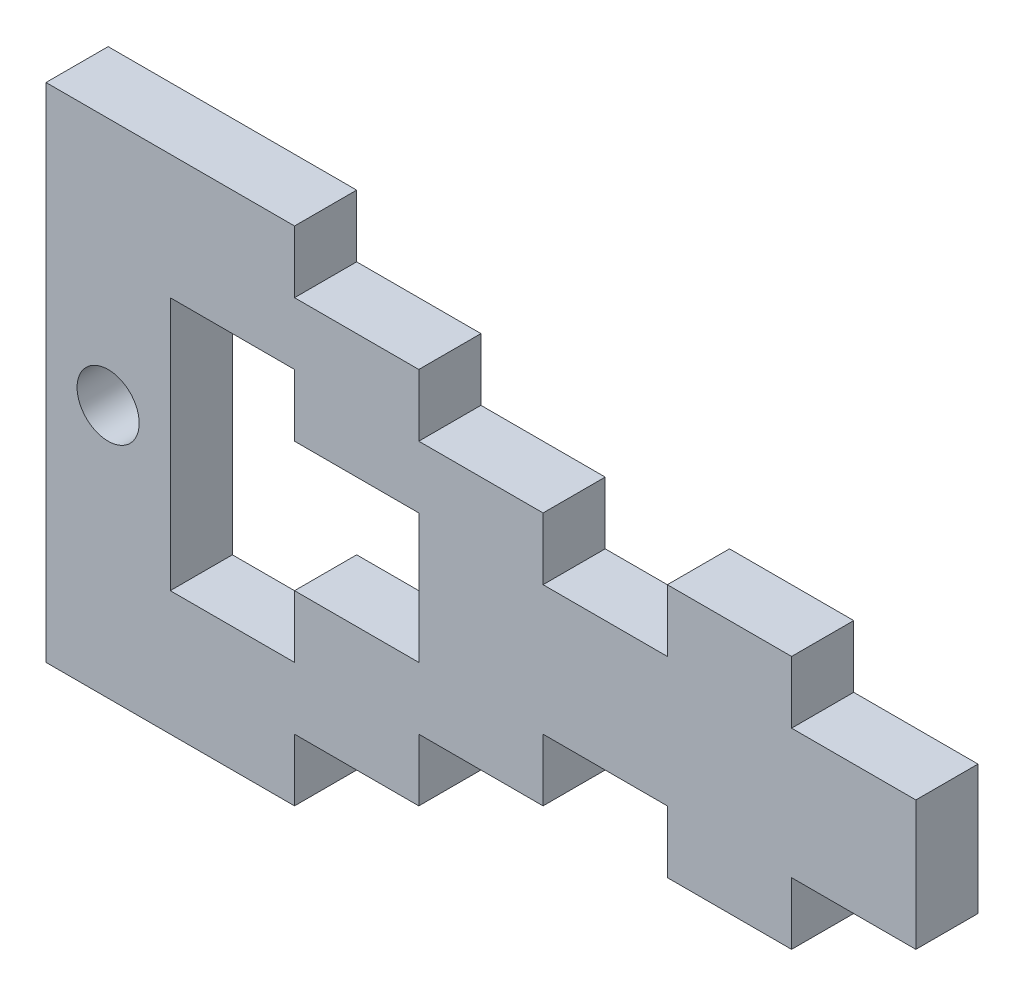
SolidWorks part; units mm, degrees
ref_plane "Front Plane" through (0, 0, 0) normal (0, 0, 1) x (1, 0, 0)
ref_plane "Top Plane" through (0, 0, 0) normal (0, 1, 0) x (1, 0, 0)
ref_plane "Right Plane" through (0, 0, 0) normal (1, 0, 0) x (0, 0, -1)
sketch "Model" plane through (0, 0, 0) normal (0, 0, 1) x (1, 0, 0)
  line L0 (3258.1067, 1248.3884) -> (3264.1067, 1248.3884)
  line L1 (3264.1067, 1242.1384) -> (3258.1067, 1242.1384)
  line L2 (3258.1067, 1248.3884) -> (3258.1067, 1251.3884)
  line L3 (3258.1067, 1251.3884) -> (3252.1067, 1251.3884)
  line L4 (3258.1067, 1242.1384) -> (3258.1067, 1239.1384)
  line L5 (3258.1067, 1239.1384) -> (3252.1067, 1239.1384)
  line L6 (3252.1067, 1251.3884) -> (3252.1067, 1248.3884)
  line L7 (3252.1067, 1248.3884) -> (3246.1067, 1248.3884)
  line L8 (3252.1067, 1239.1384) -> (3252.1067, 1242.1384)
  line L9 (3252.1067, 1242.1384) -> (3246.1067, 1242.1384)
  line L10 (3246.1067, 1248.3884) -> (3246.1067, 1251.3884)
  line L11 (3246.1067, 1251.3884) -> (3240.1067, 1251.3884)
  line L12 (3246.1067, 1242.1384) -> (3246.1067, 1239.1384)
  line L13 (3246.1067, 1239.1384) -> (3240.1067, 1239.1384)
  line L14 (3240.1067, 1248.3884) -> (3234.1067, 1248.3884)
  line L15 (3234.1067, 1242.1384) -> (3240.1067, 1242.1384)
  line L16 (3240.1067, 1251.3884) -> (3240.1067, 1254.3884)
  line L17 (3240.1067, 1254.3884) -> (3234.1067, 1254.3884)
  line L18 (3240.1067, 1239.1384) -> (3240.1067, 1236.1384)
  line L19 (3240.1067, 1236.1384) -> (3234.1067, 1236.1384)
  line L20 (3234.1067, 1254.3884) -> (3234.1067, 1257.3884)
  line L21 (3234.1067, 1257.3884) -> (3228.1067, 1257.3884)
  line L22 (3234.1067, 1236.1384) -> (3234.1067, 1233.1384)
  line L23 (3234.1067, 1233.1384) -> (3228.1067, 1233.1384)
  line L24 (3234.1067, 1248.3884) -> (3234.1067, 1251.3884)
  line L25 (3234.1067, 1251.3884) -> (3228.1067, 1251.3884)
  line L26 (3228.1067, 1239.1384) -> (3234.1067, 1239.1384)
  line L27 (3234.1067, 1239.1384) -> (3234.1067, 1242.1384)
  line L28 (3228.1067, 1257.3884) -> (3222.1067, 1257.3884)
  line L29 (3222.1067, 1233.1384) -> (3228.1067, 1233.1384)
  line L30 (3228.1067, 1251.3884) -> (3228.1067, 1245.3884)
  line L31 (3222.1067, 1257.3884) -> (3222.1067, 1245.3884)
  line L32 (3264.1067, 1245.3884) -> (3264.1067, 1248.3884)
  line L33 (3222.1067, 1233.1384) -> (3222.1067, 1245.3884)
  line L34 (3228.1067, 1239.1384) -> (3228.1067, 1245.3884)
  line L35 (3264.1067, 1242.1384) -> (3264.1067, 1245.3884)
  line L36 (3240.1067, 1248.3884) -> (3240.1067, 1242.1384)
  circle A0 centre (3225.1067, 1245.3884) radius 1.5
extrude "Boss-Extrude1" add sketch "Model" along normal blind 3 contours A0 | L36 L14 L24 L25 L30 L34 L26 L27 L15 | L31 L33 L29 L23 L22 L19 L18 L13 L12 L9 L8 L5 L4 L1 L35 L32 L0 L2 L3 L6 L7 L10 L11 L16 L17 L20 L21 L28
